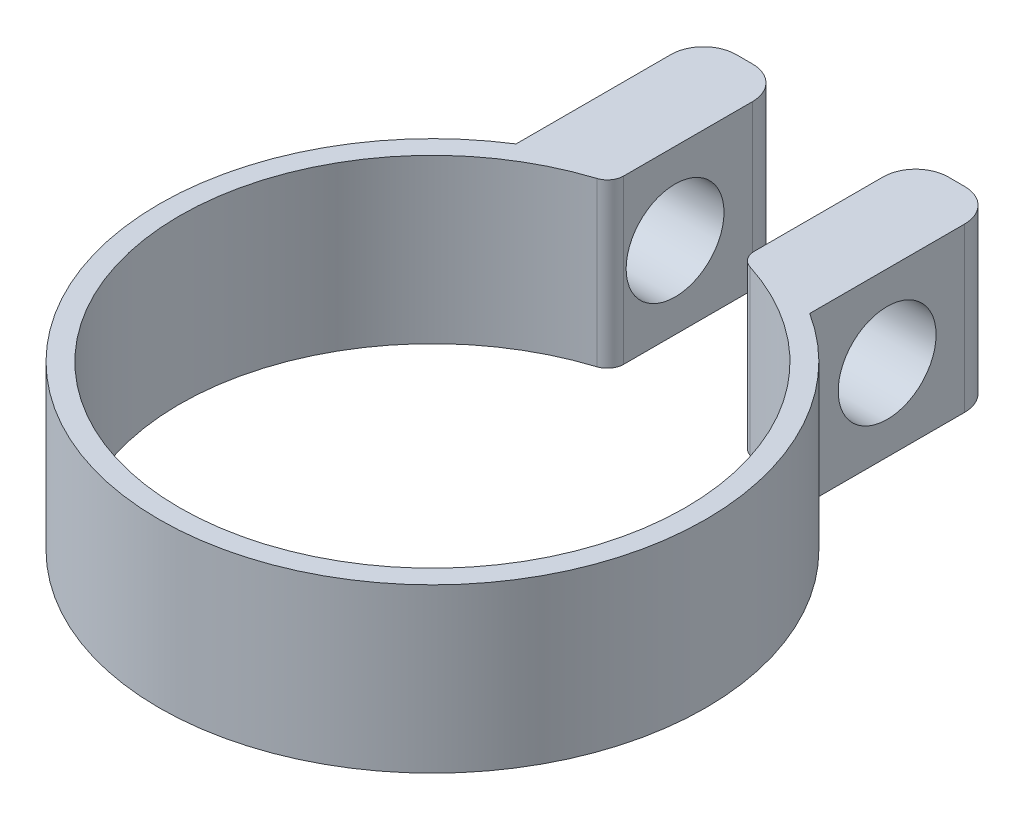
SolidWorks part; units mm, degrees
material "AISI 304"
ref_plane "Alzado" through (0, 0, 0) normal (0, 0, 1) x (1, 0, 0)
ref_plane "Planta" through (0, 0, 0) normal (0, 1, 0) x (1, 0, 0)
ref_plane "Vista lateral" through (0, 0, 0) normal (1, 0, 0) x (0, 0, -1)
sketch "Croquis1" plane through (0, 0, 0) normal (0, 1, 0) x (1, 0, 0)
  line L0 (0, 16.75) -> (0, 20.75) construction
  line L3 (-9, 14.1267) -> (-9, 25.6194)
  line L4 (-9, 25.6194) -> (-4, 25.6194)
  line L5 (-4, 14.975) -> (-4, 25.6194)
  line L7 (9, 14.1267) -> (9, 25.6194)
  line L8 (9, 25.6194) -> (4, 25.6194)
  line L9 (4, 14.975) -> (4, 25.6194)
  arc A0 (-9, 14.1267) -> (9, 14.1267) centre (0, 0) ccw
  arc A1 (-4, 14.975) -> (4, 14.975) centre (0, 0) ccw
  dimension "D1" = 33.5
  dimension "D2" = 31
  dimension "D3" = 4
  dimension "D4" = 4
  dimension "D5" = 5
  dimension "D6" = 5
extrude "Saliente-Extruir1" add sketch "Croquis1" along normal blind 10
fillet "Redondeo1" radius 1 2 edges at (4, 5, -14.975) (-4, 5, -14.975)
fillet "Redondeo2" radius 2 4 edges at (9, 5, -25.6194) (4, 5, -25.6194) (-4, 5, -25.6194) (-9, 5, -25.6194)
sketch "Croquis2" plane through (9, 0, 0) normal (1, 0, 0) x (0, 0, -1)
  line L0 (18.873, 10) -> (18.873, 0) construction
  line L1 (14.1267, 10) -> (23.6194, 10) construction
  line L2 (14.1267, 0) -> (23.6194, 0) construction
  circle A0 centre (18.873, 5) radius 3
  dimension "D1" = 6
extrude "Cortar-Extruir1" cut sketch "Croquis2" against normal through all
